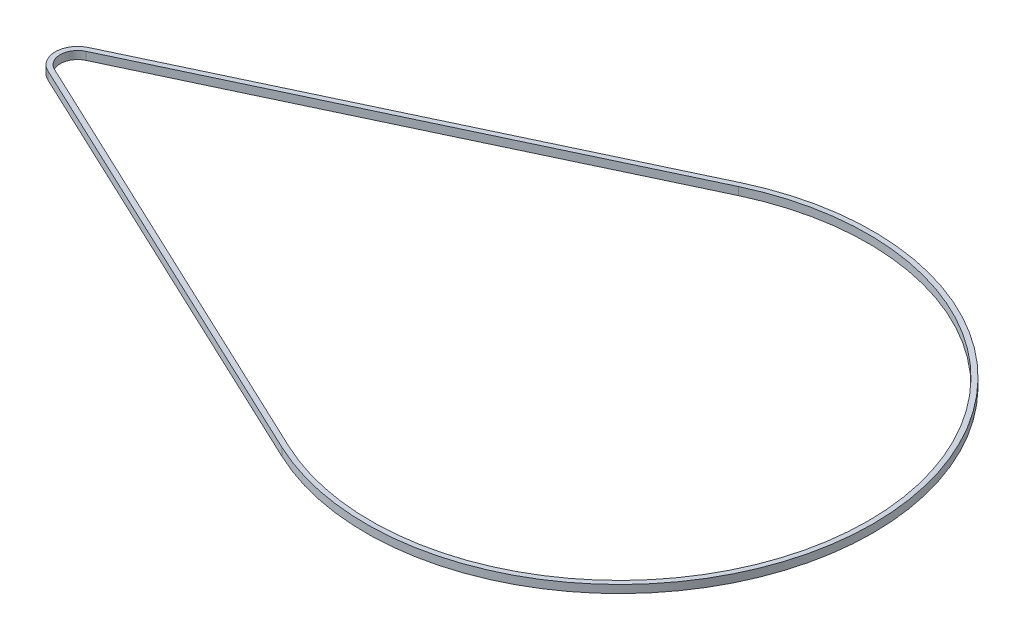
SolidWorks part; units mm, degrees
material "Rubber"
ref_plane "Front Plane" through (0, 0, 0) normal (0, 0, 1) x (1, 0, 0)
ref_plane "Top Plane" through (0, 0, 0) normal (0, 1, 0) x (1, 0, 0)
ref_plane "Right Plane" through (0, 0, 0) normal (1, 0, 0) x (0, 0, -1)
sketch "Sketch1" plane through (0, 0, 0) normal (0, 1, 0) x (1, 0, 0)
  line L0 (0, 0) -> (-218, 0) construction
  line L1 (-42.6606, 90.4438) -> (-220.9862, 6.3311)
  line L2 (-220.9862, -6.3311) -> (-42.6606, -90.4438)
  line L3 (-43.5138, 92.2527) -> (-221.8394, 8.1399)
  line L4 (-221.8394, -8.1399) -> (-43.5138, -92.2527)
  arc A0 (-42.6606, -90.4438) -> (-42.6606, 90.4438) centre (0, 0) ccw
  arc A1 (-220.9862, 6.3311) -> (-220.9862, -6.3311) centre (-218, 0) ccw
  arc A2 (-221.8394, 8.1399) -> (-221.8394, -8.1399) centre (-218, 0) ccw
  arc A3 (-43.5138, -92.2527) -> (-43.5138, 92.2527) centre (0, 0) ccw
  dimension "D1" = 100
  dimension "D2" = 7
  dimension "D3" = 218
  dimension "D4" = 2
extrude "Boss-Extrude1" add sketch "Sketch1" along normal blind 3.175
